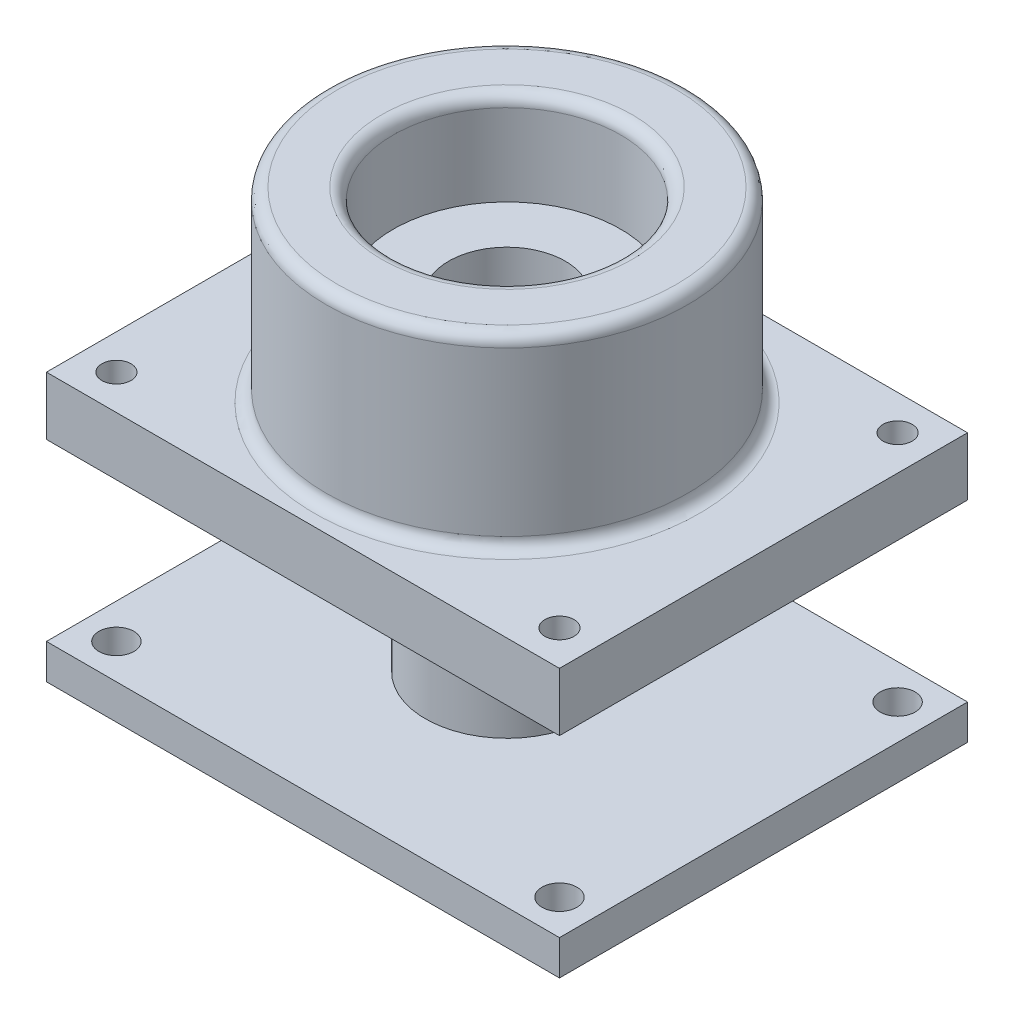
SolidWorks part; units mm, degrees
ref_plane "Front Plane" through (0, 0, 0) normal (0, 0, 1) x (1, 0, 0)
ref_plane "Top Plane" through (0, 0, 0) normal (0, 1, 0) x (1, 0, 0)
ref_plane "Right Plane" through (0, 0, 0) normal (1, 0, 0) x (0, 0, -1)
sketch "Sketch1" plane through (0, 0, 0) normal (0, 1, 0) x (1, 0, 0)
  circle A0 centre (0, 0) radius 15.5
  dimension "D1" = 31
extrude "Boss-Extrude1" add sketch "Sketch1" along normal blind 16
ref_plane "Plane1" through (0, 0, 0) normal (0, -1, 0) x (-1, 0, 0)
sketch "Sketch16" plane through (0, 0, 0) normal (0, -1, 0) x (1, 0, 0)
  line L0 (0, 0) -> (22, 17.5) construction
  line L1 (-22, 17.5) -> (22, 17.5)
  line L2 (-22, 17.5) -> (-22, -17.5)
  line L3 (-22, -17.5) -> (22, -17.5)
  line L4 (22, 17.5) -> (22, -17.5)
  line L5 (-22, 17.5) -> (22, -17.5) construction
  circle A3 centre (-19, 14.5) radius 1.25
  circle A6 centre (19, 14.5) radius 1.25
  circle A7 centre (19, -14.5) radius 1.25
  circle A8 centre (-19, -14.5) radius 1.25
  point P0 (0, 0)
  dimension "D3" = 2
  dimension "D5" = 2.5
  dimension "D8" = 3
  dimension "D1" = 35
  dimension "D2" = 44
  dimension "D4" = 2
  dimension "D9" = 3
extrude "Boss-Extrude6" add sketch "Sketch16" along normal blind 5
sketch "Sketch17" plane through (0, 16, 0) normal (0, 1, 0) x (1, 0, 0)
  circle A0 centre (0, 0) radius 9.75
  dimension "D1" = 19.5
extrude "Cut-Extrude5" cut sketch "Sketch17" against normal blind 6
sketch "Sketch18" plane through (0, 10, 0) normal (0, 1, 0) x (1, 0, 0)
  circle A0 centre (0, 0) radius 5
  dimension "D1" = 10
extrude "Cut-Extrude7" cut sketch "Sketch18" against normal blind 19
fillet "Fillet4" radius 1 1 edges at (0, 0, 15.5)
fillet "Fillet1" radius 1 1 edges at (0, 16, 9.75)
fillet "Fillet3" radius 1 1 edges at (0, 16, 15.5)
sketch "Sketch2" plane through (0, 0, 0) normal (0, -1, 0) x (-1, 0, 0)
  circle A0 centre (0, 0) radius 7
  dimension "D1" = 14
extrude "Boss-Extrude3" add sketch "Sketch2" along normal blind 20 contours A0
ref_plane "Plane3" through (0, 16, 0) normal (0, 1, 0) x (1, 0, 0)
sketch "Sketch5" plane through (0, 16, 0) normal (0, 1, 0) x (1, 0, 0)
  circle A0 centre (0, 0) radius 9.75
  dimension "D1" = 19.5
extrude "Cut-Extrude1" cut sketch "Sketch5" against normal blind 8
ref_plane "Plane4" through (0, 8, 0) normal (0, 1, 0) x (1, 0, 0)
sketch "Sketch6" plane through (0, 8, 0) normal (0, 1, 0) x (1, 0, 0)
  circle A0 centre (0, 0) radius 5
  dimension "D1" = 10
extrude "Cut-Extrude2" cut sketch "Sketch6" against normal blind 30
ref_plane "Plane10" through (0, -20, 0) normal (0, -1, 0) x (-1, 0, 0)
sketch "Sketch12" plane through (0, -20, 0) normal (0, -1, 0) x (-1, 0, 0)
  line L1 (-22, 17.5) -> (22, 17.5)
  line L2 (-22, 17.5) -> (-22, -17.5)
  line L3 (-22, -17.5) -> (22, -17.5)
  line L4 (22, 17.5) -> (22, -17.5)
  line L5 (-22, 17.5) -> (22, -17.5) construction
  line L6 (-22, -17.5) -> (22, 17.5) construction
  circle A1 centre (-19, -14.5) radius 1.5
  circle A2 centre (19, -14.5) radius 1.5
  circle A3 centre (19, 14.5) radius 1.5
  circle A4 centre (-19, 14.5) radius 1.5
  point P0 (0, 0)
  dimension "D1" = 44
  dimension "D3" = 3
  dimension "D2" = 35
  dimension "D4" = 3
  dimension "D5" = 2
  dimension "D6" = 2
extrude "Boss-Extrude4" add sketch "Sketch12" along normal blind 3 contours L2 L3 L4 L1
sketch "Sketch14" plane through (0, -20, 0) normal (0, -1, 0) x (-1, 0, 0)
  line L0 (-22, -17.5) -> (22, -17.5) construction
  line L1 (-22, 17.5) -> (-22, -17.5) construction
  circle A0 centre (-19, -14.5) radius 1.5
  circle A1 centre (19, -14.5) radius 1.5
  circle A2 centre (19, 14.5) radius 1.5
  circle A3 centre (-19, 14.5) radius 1.5
  dimension "D1" = 3
  dimension "D3" = 3
  dimension "D2" = 3
  dimension "D4" = 2
  dimension "D5" = 2
extrude "Cut-Extrude3" cut sketch "Sketch14" along normal blind 3
sketch "Sketch15" plane through (0, -20, 0) normal (0, -1, 0) x (-1, 0, 0)
  circle A0 centre (0, 0) radius 5
  dimension "D1" = 10
extrude "Cut-Extrude4" cut sketch "Sketch15" along normal blind 3
